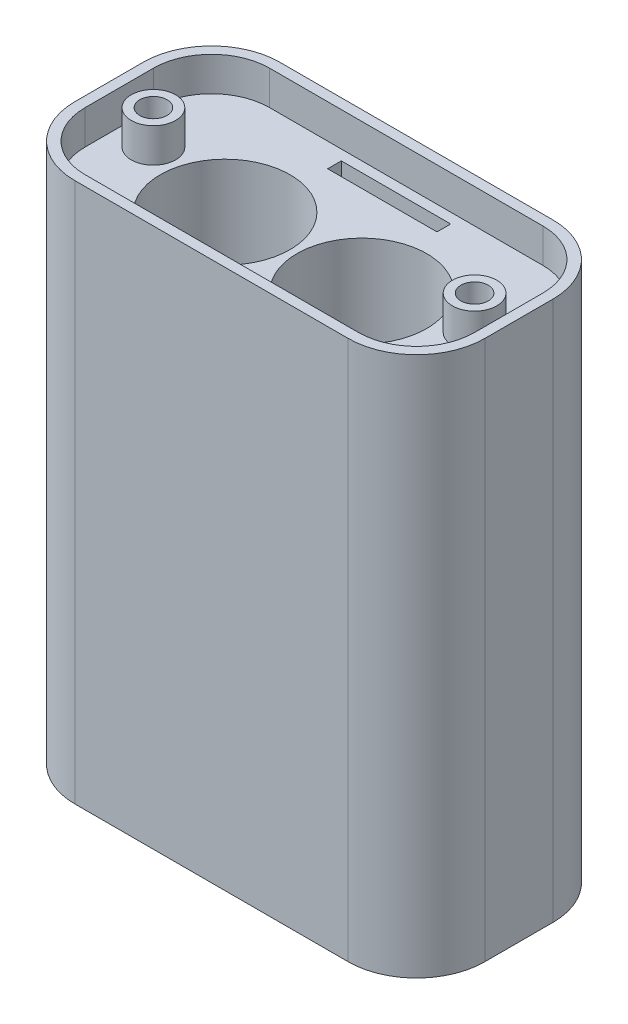
SolidWorks part; units mm, degrees
ref_plane "Спереди" through (0, 0, 0) normal (0, 0, 1) x (1, 0, 0)
ref_plane "Сверху" through (0, 0, 0) normal (0, 1, 0) x (1, 0, 0)
ref_plane "Справа" through (0, 0, 0) normal (1, 0, 0) x (0, 0, -1)
sketch "Эскиз1" plane through (0, 0, 0) normal (0, 1, 0) x (1, 0, 0)
  line L0 (-72.8908, 0) -> (73.0919, 0) construction
  line L1 (0, 46.6177) -> (0, -43.256) construction
  line L3 (-20, 18) -> (20, 18)
  line L4 (-30, 8) -> (-30, -2)
  line L5 (-20, -12) -> (20, -12)
  line L6 (30, 8) -> (30, -2)
  circle A0 centre (-10, 0) radius 9.5
  circle A1 centre (10, 0) radius 9.5
  arc A2 (20, 18) -> (30, 8) centre (20, 8) cw
  arc A3 (20, -12) -> (30, -2) centre (20, -2) ccw
  arc A4 (-30, -2) -> (-20, -12) centre (-20, -2) ccw
  arc A5 (-20, 18) -> (-30, 8) centre (-20, 8) ccw
  point P19 (-30, -12)
  point P22 (-30, 18)
  dimension "D1" = 19
  dimension "D2" = 10
  dimension "D3" = 18
  dimension "D7" = 10
  dimension "D4" = 30
  dimension "D5" = 30
  dimension "D6" = 30
extrude "Бобышка-Вытянуть1" add sketch "Эскиз1" along normal blind 10
sketch "Эскиз2" plane through (0, 10, 0) normal (0, 1, 0) x (1, 0, 0)
  line L0 (-20, -12) -> (20, -12) construction
  line L1 (30, -2) -> (30, 8) construction
  line L2 (20, 18) -> (-20, 18) construction
  line L3 (-20, -12) -> (20, -12)
  line L4 (30, -2) -> (30, 8)
  line L5 (20, 18) -> (-20, 18)
  line L6 (-30, 8) -> (-30, -2) construction
  line L7 (-30, 8) -> (-30, -2)
  line L8 (-20, 16.5) -> (20, 16.5)
  line L9 (-20, -10.5) -> (20, -10.5)
  line L10 (-20, 16.5) -> (-20, -10.5) construction
  line L11 (-28.5, 8) -> (-28.5, -2)
  line L12 (0, 19.9133) -> (0, -21.3858) construction
  line L13 (28.5, 8) -> (28.5, -2)
  arc A0 (-30, -2) -> (-20, -12) centre (-20, -2) ccw construction
  arc A1 (20, -12) -> (30, -2) centre (20, -2) ccw construction
  arc A2 (30, 8) -> (20, 18) centre (20, 8) ccw construction
  arc A3 (-20, 18) -> (-30, 8) centre (-20, 8) ccw construction
  arc A4 (-30, -2) -> (-20, -12) centre (-20, -2) ccw
  arc A5 (20, -12) -> (30, -2) centre (20, -2) ccw
  arc A6 (30, 8) -> (20, 18) centre (20, 8) ccw
  arc A7 (-20, 18) -> (-30, 8) centre (-20, 8) ccw
  circle A8 centre (-20, 8) radius 8.5
  circle A9 centre (-20, -2) radius 8.5
  circle A10 centre (20, 8) radius 8.5
  circle A11 centre (20, -2) radius 8.5
  point P24 (0, 16.5)
  point P29 (0, -10.5)
  circle M13 centre (-10, 0) radius 9.5
  circle M14 centre (10, 0) radius 9.5
  dimension "D1" = 1.5
  dimension "D2" = 1.5
extrude "Вырез-Вытянуть1" cut sketch "Эскиз2" against normal blind 5 contours A9 A8 M13 | L9 A11 A10 L8 A8 A9 M14 M13 | A9 A8 M13 | A9 A8 M13 | A9 A8 L11 | A11 A10 M14 | A11 A10 M14 | A11 A10 M14 | A10 A11 L13
sketch "Эскиз3" plane through (0, 5, 0) normal (0, 1, 0) x (1, 0, 0)
  line L0 (-28.5, 3) -> (28.9714, 3) construction
  line L1 (-30, 8) -> (-30, -2) construction
  line L2 (0, 16.5) -> (0, -10.5) construction
  line L3 (-20, 16.5) -> (20, 16.5) construction
  line L4 (-20, -10.5) -> (20, -10.5) construction
  line L5 (-28.5, 8) -> (-28.5, -2) construction
  circle A0 centre (-23.5, 3) radius 3.25
  circle A1 centre (-23.5, 3) radius 2
  circle A2 centre (23.5, 3) radius 3.25
  circle A3 centre (23.5, 3) radius 2
  dimension "D1" = 6.5
  dimension "D2" = 6.5
  dimension "D3" = 4
extrude "Бобышка-Вытянуть2" add sketch "Эскиз3" along normal blind 5
sketch "Эскиз4" plane through (0, 5, 0) normal (0, 1, 0) x (1, 0, 0)
  line L0 (0, 16.5) -> (0, -10.5) construction
  line L1 (-8, 15) -> (8, 15)
  line L2 (-8, 15) -> (-8, 13)
  line L3 (-8, 13) -> (8, 13)
  line L4 (8, 15) -> (8, 13)
  line L5 (-20, 16.5) -> (20, 16.5) construction
  line L6 (-20, -10.5) -> (20, -10.5) construction
  line L7 (-28.5, 3) -> (28.5, 3) construction
  line L8 (-28.5, 8) -> (-28.5, -2) construction
  line L9 (28.5, 8) -> (28.5, -2) construction
  point P10 (0, 13)
  dimension "D1" = 2
  dimension "D2" = 8
  dimension "D3" = 1.5
extrude "Вырез-Вытянуть2" cut sketch "Эскиз4" against normal through all
sketch "Эскиз5" plane through (0, 0, 0) normal (0, -1, 0) x (1, 0, 0)
  line L4 (30, -8) -> (30, 2)
  line L5 (20, 12) -> (-20, 12)
  line L6 (-30, 2) -> (-30, -8)
  line L7 (-20, -18) -> (20, -18)
  line L8 (30, -8) -> (30, 2)
  line L9 (20, 12) -> (-20, 12)
  line L10 (-30, 2) -> (-30, -8)
  line L11 (-20, -18) -> (20, -18)
  arc A4 (20, -18) -> (30, -8) centre (20, -8) ccw
  arc A5 (30, 2) -> (20, 12) centre (20, 2) ccw
  arc A6 (-20, 12) -> (-30, 2) centre (-20, 2) ccw
  arc A7 (-30, -8) -> (-20, -18) centre (-20, -8) ccw
  arc A8 (20, -18) -> (30, -8) centre (20, -8) ccw
  arc A9 (30, 2) -> (20, 12) centre (20, 2) ccw
  arc A10 (-20, 12) -> (-30, 2) centre (-20, 2) ccw
  arc A11 (-30, -8) -> (-20, -18) centre (-20, -8) ccw
  dimension "D1" = 0
extrude "Бобышка-Вытянуть3" add sketch "Эскиз5" along normal blind 29.5
ref_plane "Плоскость1" through (0, -29.5, 0) normal (0, -1, 0) x (-1, 0, 0)
mirror "Зеркальное отражение5" about plane through (0, -29.5, 0) normal (0, -1, 0) of "Бобышка-Вытянуть3", "Вырез-Вытянуть2", "Бобышка-Вытянуть2", "Вырез-Вытянуть1", "Бобышка-Вытянуть1"
sketch "Эскиз8" plane through (0, 0, -18) normal (0, 0, -1) x (-1, 0, 0)
  line L0 (-20, 10) -> (-20, -69) construction
  line L1 (-20, 0) -> (20, 0)
  line L2 (-20, 0) -> (-20, -59)
  line L3 (-20, -59) -> (20, -59)
  line L4 (20, 0) -> (20, -59)
  line L5 (20, 10) -> (20, -69) construction
  line L6 (-20, 10) -> (20, 10) construction
  line L7 (-20, -69) -> (20, -69) construction
  dimension "D1" = 10
  dimension "D2" = 10
extrude "Вырез-Вытянуть4" cut sketch "Эскиз8" against normal blind 8
sketch "Эскиз9" plane through (0, -59, 0) normal (0, -1, 0) x (-1, 0, 0)
  circle A0 centre (10, 0) radius 9.5 construction
  circle A1 centre (-10, 0) radius 9.5 construction
  circle A2 centre (10, 0) radius 9.5
  circle A3 centre (-10, 0) radius 9.5
extrude "Вырез-Вытянуть5" cut sketch "Эскиз9" against normal through all
sketch "Эскиз10" plane through (0, 0, -10) normal (0, 0, -1) x (-1, 0, 0)
  line L2 (-20, 0) -> (-20, -59) construction
  line L3 (-20, -59) -> (20, -59) construction
  line L4 (0, -59) -> (0, 0) construction
  line L5 (-20, -59) -> (20, -59) construction
  line L6 (-20, -29.5) -> (20, -29.5) construction
  line L7 (20, -59) -> (20, 0) construction
  circle A0 centre (-13.5, -52.5) radius 3.25
  circle A1 centre (-13.5, -52.5) radius 2
  circle A2 centre (13.5, -52.5) radius 2
  circle A3 centre (13.5, -52.5) radius 3.25
  circle A4 centre (13.5, -6.5) radius 2
  circle A5 centre (13.5, -6.5) radius 3.25
  circle A6 centre (-13.5, -6.5) radius 2
  circle A7 centre (-13.5, -6.5) radius 3.25
  dimension "D1" = 6.5
  dimension "D2" = 4
  dimension "D3" = 6.5
  dimension "D4" = 6.5
extrude "Бобышка-Вытянуть4" add sketch "Эскиз10" along normal blind 6
sketch "Эскиз11" plane through (0, 0, -10) normal (0, 0, -1) x (-1, 0, 0)
  line L0 (-20, 0) -> (-20, -59) construction
  line L5 (-20, -59) -> (20, -59) construction
  line L6 (20, -59) -> (20, 0) construction
  line L7 (20, 0) -> (-20, 0) construction
  line L8 (-20, -59) -> (20, -59)
  line L9 (20, -59) -> (20, 0)
  line L10 (20, 0) -> (-20, 0)
  line L11 (-20, 0) -> (-20, -59)
  circle A0 centre (-13.5, -52.5) radius 3.25 construction
  circle A1 centre (-13.5, -52.5) radius 3.25
  circle A2 centre (13.5, -52.5) radius 3.25 construction
  circle A3 centre (13.5, -6.5) radius 3.25 construction
  circle A4 centre (-13.5, -6.5) radius 3.25 construction
  circle A5 centre (13.5, -52.5) radius 3.25
  circle A6 centre (13.5, -6.5) radius 3.25
  circle A7 centre (-13.5, -6.5) radius 3.25
